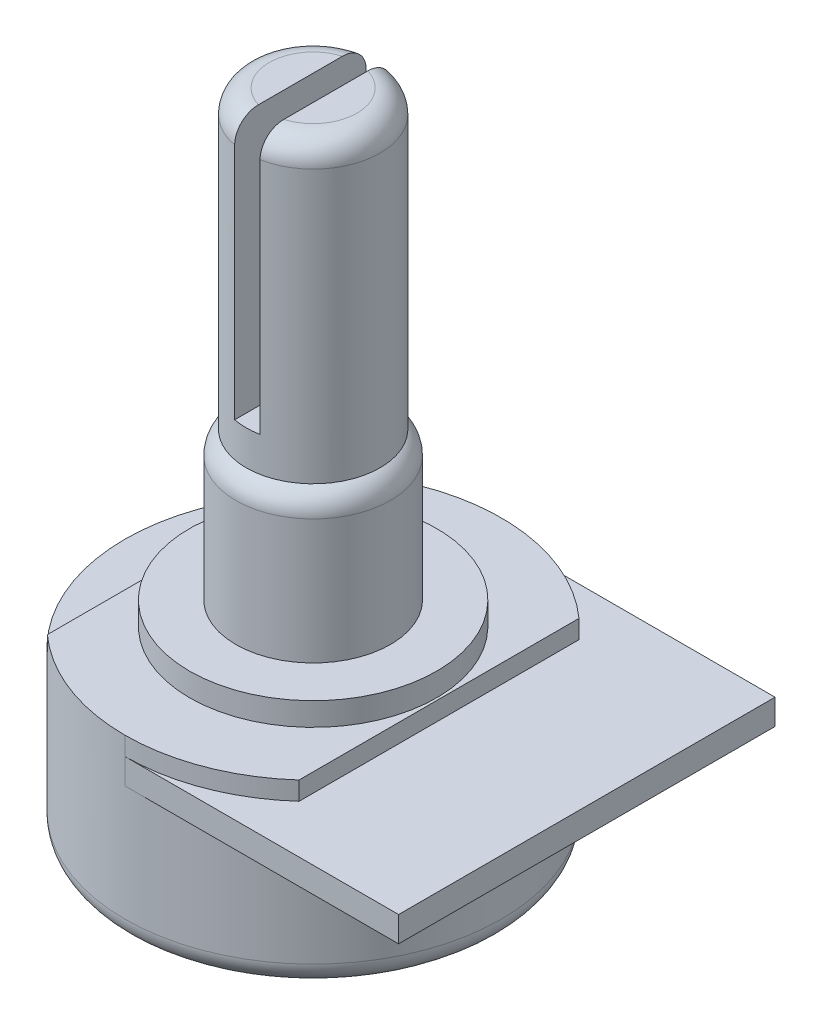
SolidWorks part; units mm, degrees
ref_plane "Спереди" through (0, 0, 0) normal (0, 0, 1) x (1, 0, 0)
ref_plane "Сверху" through (0, 0, 0) normal (0, 1, 0) x (1, 0, 0)
ref_plane "Справа" through (0, 0, 0) normal (1, 0, 0) x (0, 0, -1)
sketch "Sketch1" plane through (0, 0, 0) normal (0, 1, 0) x (1, 0, 0)
  circle A0 centre (0, 0) radius 8.15
  dimension "D1" = 16.3
extrude "Boss-Extrude1" add sketch "Sketch1" along normal blind 6
sketch "Sketch2" plane through (0, 6, 0) normal (0, 1, 0) x (1, 0, 0)
  line L0 (0, -8.15) -> (11.85, -8.15)
  line L1 (11.85, -8.15) -> (11.85, 8.15)
  line L2 (11.85, 8.15) -> (0, 8.15)
  line L3 (11.85, 0) -> (-8.15, 0) construction
  arc A0 (0, 8.15) -> (0, -8.15) centre (0, 0) ccw
  circle A1 centre (0, 0) radius 8.15 construction
  point P3 (-8.15, 0)
  point P8 (11.85, 0)
  dimension "D1" = 20
extrude "Boss-Extrude2" add sketch "Sketch2" along normal blind 1.1
sketch "Sketch3" plane through (0, 7.1, 0) normal (0, 1, 0) x (1, 0, 0)
  line L0 (-5.45, 6.0597) -> (-5.45, -6.0597)
  line L1 (5.45, -6.0597) -> (5.45, 6.0597)
  line L2 (-5.45, 0) -> (5.45, 0) construction
  arc A0 (0, 8.15) -> (0, -8.15) centre (0, 0) ccw construction
  circle A1 centre (0, 0) radius 8.15 construction
  arc A2 (-5.45, -6.0597) -> (5.45, -6.0597) centre (0, 0) ccw
  arc A3 (5.45, 6.0597) -> (-5.45, 6.0597) centre (0, 0) ccw
  dimension "D1" = 10.9
extrude "Boss-Extrude3" add sketch "Sketch3" along normal blind 0.8
sketch "Sketch4" plane through (0, 7.9, 0) normal (0, 1, 0) x (1, 0, 0)
  circle A0 centre (0, 0) radius 5.35
  dimension "D1" = 10.7
extrude "Boss-Extrude4" add sketch "Sketch4" along normal blind 1
sketch "Sketch5" plane through (0, 8.9, 0) normal (0, 1, 0) x (1, 0, 0)
  circle A0 centre (0, 0) radius 3.35
  dimension "D1" = 6.7
extrude "Boss-Extrude5" add sketch "Sketch5" along normal blind 6.4
fillet "Fillet1" radius 1 2 edges at (0, 0, 8.15) (0, 15.3, 3.35)
sketch "Sketch6" plane through (0, 15.3, 0) normal (0, 1, 0) x (1, 0, 0)
  circle A0 centre (0, 0) radius 2.9
  dimension "D1" = 5.8
extrude "Boss-Extrude6" add sketch "Sketch6" along normal blind 12.8
sketch "Sketch7" plane through (0, 28.1, 0) normal (0, 1, 0) x (1, 0, 0)
  line L1 (0.55, 5) -> (-0.55, 5)
  line L2 (0.55, 5) -> (0.55, -5)
  line L3 (0.55, -5) -> (-0.55, -5)
  line L4 (-0.55, 5) -> (-0.55, -5)
  line L5 (0.55, 5) -> (-0.55, -5) construction
  line L6 (0.55, -5) -> (-0.55, 5) construction
  point P0 (0, 0)
  dimension "D1" = 1.1
  dimension "D2" = 10
extrude "Cut-Extrude1" cut sketch "Sketch7" against normal blind 11.3
fillet "Fillet2" radius 1 2 edges at (2.9, 28.1, 0) (-2.9, 28.1, 0)
